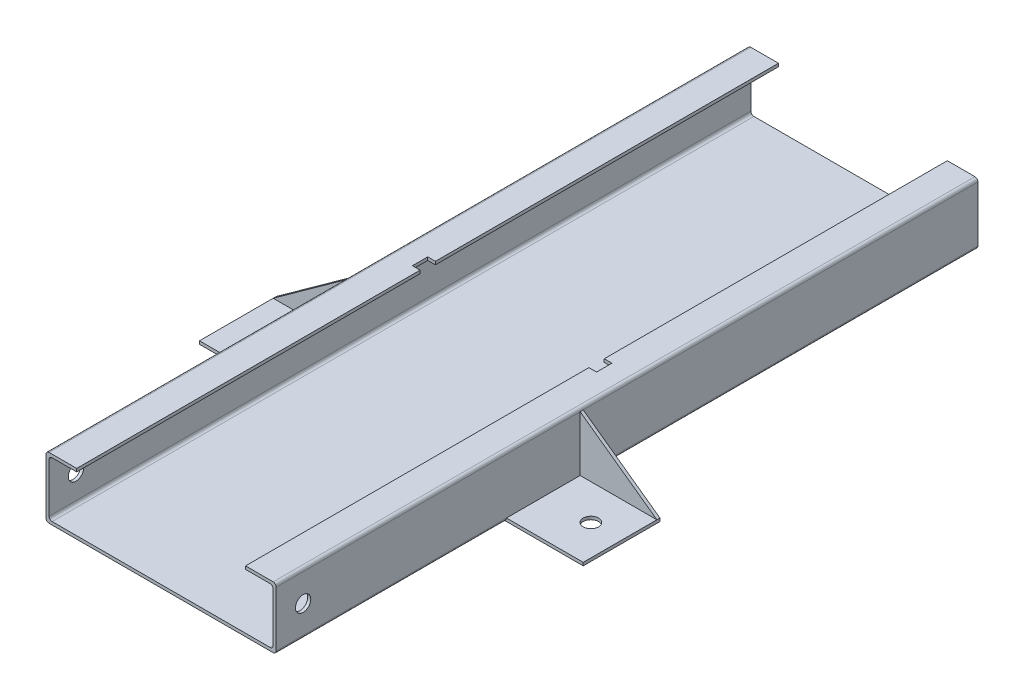
SolidWorks part; units mm, degrees
ref_plane "Alzado" through (0, 0, 0) normal (0, 0, 1) x (1, 0, 0)
ref_plane "Planta" through (0, 0, 0) normal (0, 1, 0) x (1, 0, 0)
ref_plane "Vista lateral" through (0, 0, 0) normal (1, 0, 0) x (0, 0, -1)
sketch "Croquis2" plane through (0, 0, 0) normal (0, 0, 1) x (1, 0, 0)
  line L0 (-75, 20) -> (-55, 20)
  line L1 (-75, -20) -> (75, -20)
  line L2 (-75, -20) -> (-75, 20)
  line L4 (75, -20) -> (75, 20)
  line L5 (-67.6394, -18.0372) -> (-67.5, -18) construction
  line L6 (75, 20) -> (55, 20)
  line L7 (-73, -18) -> (73, -18)
  line L8 (-73, -18) -> (-73, 18)
  line L10 (73, -18) -> (73, 18)
  line L11 (-73, -18) -> (-67.6394, -18.0372) construction
  line L12 (-55, 20) -> (-55, 18)
  line L13 (-55, 18) -> (-73, 18)
  line L14 (73, 18) -> (55, 18)
  line L15 (55, 18) -> (55, 20)
  point P0 (0, 0)
  point P6 (71.25, -19)
  dimension "D1" = 150
  dimension "D2" = 40
  dimension "D3" = 146
  dimension "D4" = 36
  dimension "D5" = 20
extrude "Saliente-Extruir2" add sketch "Croquis2" along normal mid plane 457.2
fillet "Redondeo1" radius 2 8 edges at (-73, 18, 0) (73, 18, 0) (-75, -20, 0) (75, -20, 0) (75, 20, 0) (73, -18, 0) (-73, -18, 0) (-75, 20, 0)
sketch "Croquis3" plane through (75, 0, 0) normal (1, 0, 0) x (0, 0, -1)
  line L0 (-228.6, -18) -> (-228.6, 18) construction
  line L1 (-228.6, -18) -> (228.6, -18) construction
  circle A0 centre (-211.1, 0) radius 5
  dimension "D1" = 10
  dimension "D2" = 17.5
  dimension "D3" = 18
extrude "Cortar-Extruir1" cut sketch "Croquis3" against normal through all
sketch "Croquis5" plane through (75, 0, 0) normal (1, 0, 0) x (0, 0, -1)
  line L0 (228.6, -20) -> (-228.6, -20) construction
  line L1 (-78.6, -20) -> (-28.6, -20)
  line L2 (-78.6, -20) -> (-78.6, -18)
  line L3 (-78.6, -18) -> (-28.6, -18)
  line L4 (-28.6, -20) -> (-28.6, -18)
  line L5 (-228.6, -18) -> (228.6, -18) construction
  line L6 (-228.6, -18) -> (-228.6, 18) construction
  dimension "D1" = 50
  dimension "D2" = 150
extrude "Saliente-Extruir3" add sketch "Croquis5" along normal blind 50 and the other way blind 3
sketch "Croquis6" plane through (0, -18, 0) normal (0, 1, 0) x (1, 0, 0)
  line L0 (125, -28.6) -> (125, -78.6) construction
  line L1 (75, -28.6) -> (125, -28.6) construction
  circle A0 centre (105, -53.6) radius 5
  dimension "D1" = 10
  dimension "D2" = 20
  dimension "D3" = 25
extrude "Cortar-Extruir2" cut sketch "Croquis6" against normal blind 50
sketch "Croquis7" plane through (0, 0, 28.6) normal (0, 0, -1) x (-1, 0, 0)
  line L0 (-75, -18) -> (-75, 18)
  line L1 (-75, 18) -> (-125, -18)
  line L2 (-125, -18) -> (-75, -18)
extrude "Saliente-Extruir4" add sketch "Croquis7" against normal blind 2
mirror "Simetría1" about plane through (0, 0, 0) normal (1, 0, 0) of "Cortar-Extruir2", "Saliente-Extruir3", "Saliente-Extruir4"
sketch "Croquis8" plane through (0, 20, 0) normal (0, 1, 0) x (1, 0, 0)
  line L0 (-55, -228.6) -> (-55, 228.6) construction
  line L1 (-55, 5.1) -> (-60, 5.1)
  line L2 (-55, 5.1) -> (-55, -4.9)
  line L3 (-55, -4.9) -> (-60, -4.9)
  line L4 (-60, 5.1) -> (-60, -4.9)
  line L5 (-55, 228.6) -> (-73, 228.6) construction
  line L6 (0, -22) -> (0, 22) construction
  line L7 (60, 5.1) -> (60, -4.9)
  line L8 (55, -4.9) -> (60, -4.9)
  line L9 (55, 5.1) -> (55, -4.9)
  line L10 (55, 5.1) -> (60, 5.1)
  dimension "D1" = 5
  dimension "D2" = 10
  dimension "D3" = 223.5
extrude "Cortar-Extruir3" cut sketch "Croquis8" against normal blind 10
